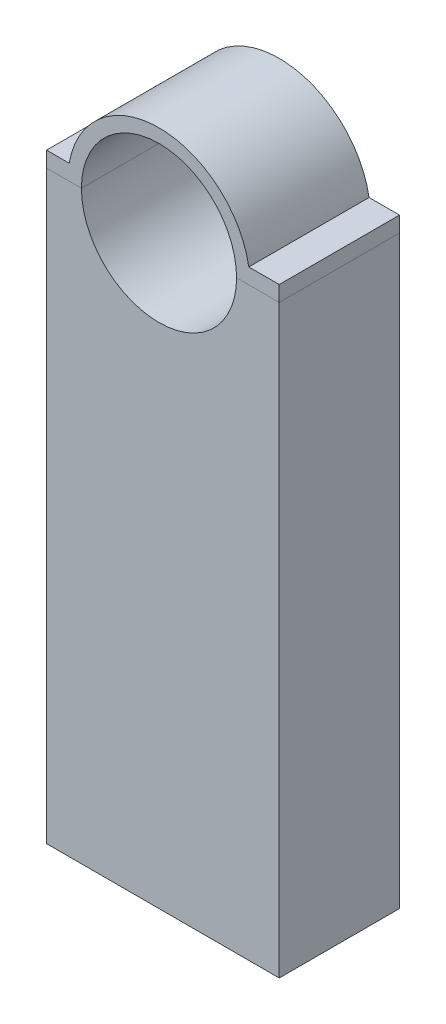
SolidWorks part; units mm, degrees
ref_plane "Front Plane" through (0, 0, 0) normal (0, 0, 1) x (1, 0, 0)
ref_plane "Top Plane" through (0, 0, 0) normal (0, 1, 0) x (1, 0, 0)
ref_plane "Right Plane" through (0, 0, 0) normal (1, 0, 0) x (0, 0, -1)
sketch "Sketch1" plane through (0, 0, 0) normal (0, 0, 1) x (1, 0, 0)
  line L0 (38.9797, 141.9959) -> (49.9797, 141.9959)
  line L1 (-10.0203, 141.9959) -> (-1.0203, 141.9959)
  line L2 (-10.0203, 141.9959) -> (-10.0203, -8.8441)
  line L3 (-10.0203, -8.8441) -> (49.9797, -8.8441)
  line L4 (49.9797, 141.9959) -> (49.9797, -8.8441)
  arc A0 (-1.0203, 141.9959) -> (38.9797, 141.9959) centre (18.9797, 141.9959) ccw
  dimension "D3" = 40
  dimension "D1" = 150.84
  dimension "D2" = 60
extrude "Boss-Extrude1" add sketch "Sketch1" along normal blind 31
sketch "Sketch2" plane through (0, 0, 31) normal (0, 0, 1) x (1, 0, 0)
  line L0 (-10.0203, 141.9959) -> (-10.0203, 145.9959)
  line L1 (-10.0203, 145.9959) -> (-4.1774, 145.9959)
  line L2 (-10.0203, 141.9959) -> (-1.0203, 141.9959)
  line L3 (42.1367, 145.9959) -> (49.9797, 145.9959)
  line L4 (49.9797, 141.9959) -> (49.9797, 145.9959)
  line L5 (38.9797, 141.9959) -> (49.9797, 141.9959)
  arc A0 (38.9797, 141.9959) -> (-1.0203, 141.9959) centre (18.9797, 141.9959) ccw
  arc A1 (42.1367, 145.9959) -> (-4.1774, 145.9959) centre (18.9797, 141.9959) ccw
  dimension "D1" = 47
  dimension "D2" = 4
  dimension "D3" = 4
extrude "Boss-Extrude2" add sketch "Sketch2" against normal blind 31 separate body
